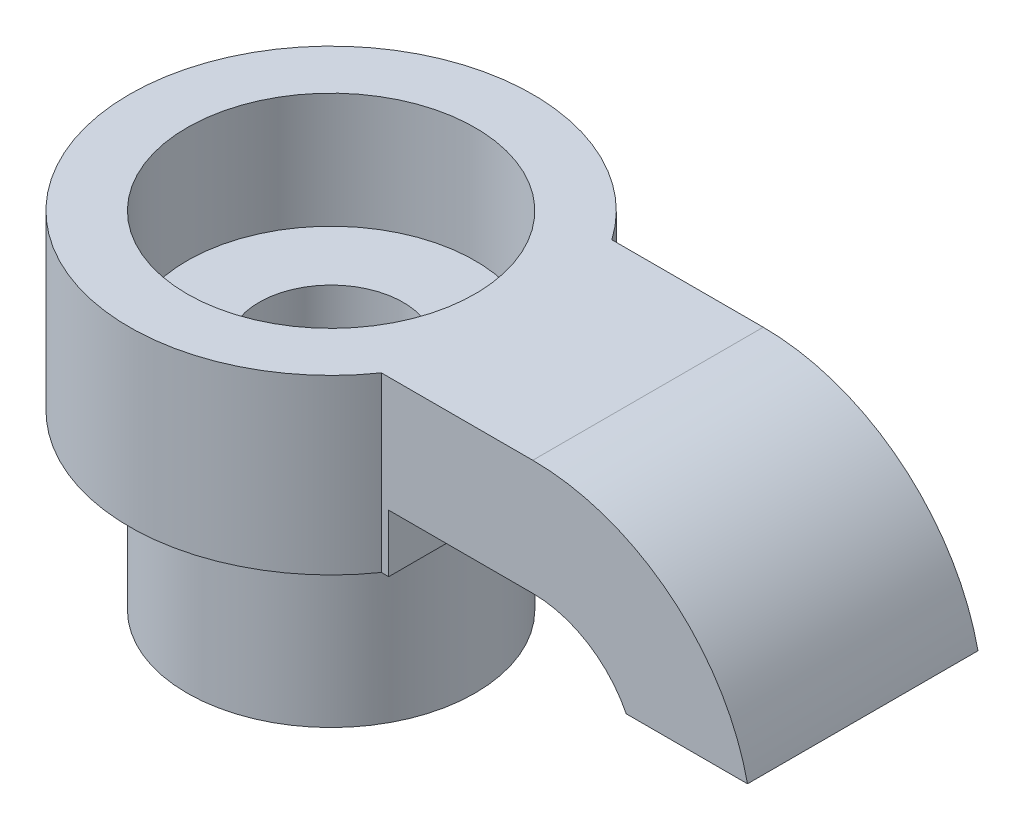
SolidWorks part; units mm, degrees
ref_plane "前视基准面" through (0, 0, 0) normal (0, 0, 1) x (1, 0, 0)
ref_plane "上视基准面" through (0, 0, 0) normal (0, 1, 0) x (1, 0, 0)
ref_plane "右视基准面" through (0, 0, 0) normal (1, 0, 0) x (0, 0, -1)
sketch "草图3" plane through (0, 0, 0) normal (0, 0, 1) x (1, 0, 0)
  line L0 (0, 0) -> (5, 0)
  line L1 (0, 0) -> (0, -4)
  line L2 (0, -4) -> (5, -4)
  line L3 (8.2435, -6) -> (12.454, -6)
  arc A0 (5, 0) -> (12.454, -6) centre (5, -7.6301) cw
  arc A1 (5, -4) -> (8.2435, -6) centre (5, -7.6301) cw
  dimension "D1" = 6
  dimension "D2" = 4
  dimension "D3" = 5
extrude "凸台-拉伸1" add sketch "草图3" along normal blind 8
sketch "草图4" plane through (0, 0, 0) normal (0, 1, 0) x (1, 0, 0)
  line L0 (0, -8) -> (0, 0) construction
  line L1 (-0.2554, 0) -> (0, 0)
  line L2 (5, 0) -> (0, 0) construction
  line L3 (0, 0) -> (0, -8)
  line L4 (0, -8) -> (-0.2554, -8)
  line L5 (5, -8) -> (0, -8) construction
  arc A0 (-0.2554, 0) -> (-0.2554, -8) centre (-6, -4) ccw
  dimension "D1" = 14
  dimension "D2" = 6
extrude "凸台-拉伸2" add sketch "草图4" against normal blind 6
sketch "草图5" plane through (0, -6, 0) normal (0, -1, 0) x (1, 0, 0)
  circle A0 centre (-6, 4) radius 5
  dimension "D1" = 10
extrude "凸台-拉伸3" add sketch "草图5" along normal blind 6
hole_wizard "孔1" positions "3D草图2" profile "草图6" legacy
sketch3d "3D草图2"
  arc A0 (-0.2554, 0, 0) -> (-0.2554, 0, 8) centre (-6, 0, 4) ccw construction
  point P0 (-6, 0, 4)
  point P6 (-6, 7, 4)
  dimension "D1" = 0
sketch "草图6" plane through (-6, 0, 4) normal (1, 0, 0) x (0, 0, 1)
  line L0 (0, 0) -> (0, 30)
  line L1 (0, 30) -> (2.5, 30)
  line L2 (2.5, 30) -> (2.5, 4)
  line L3 (2.5, 4) -> (5, 4)
  line L4 (5, 4) -> (5, 0)
  line L5 (5, 0) -> (0, 0)
  line L6 (0, 110) -> (0, -10) construction
  dimension "直径" = 5
  dimension "深度" = 30
  dimension "柱坑直径" = 10
  dimension "柱坑深度" = 4
cosmetic thread "装饰螺纹线1" parameters "D2"=15
